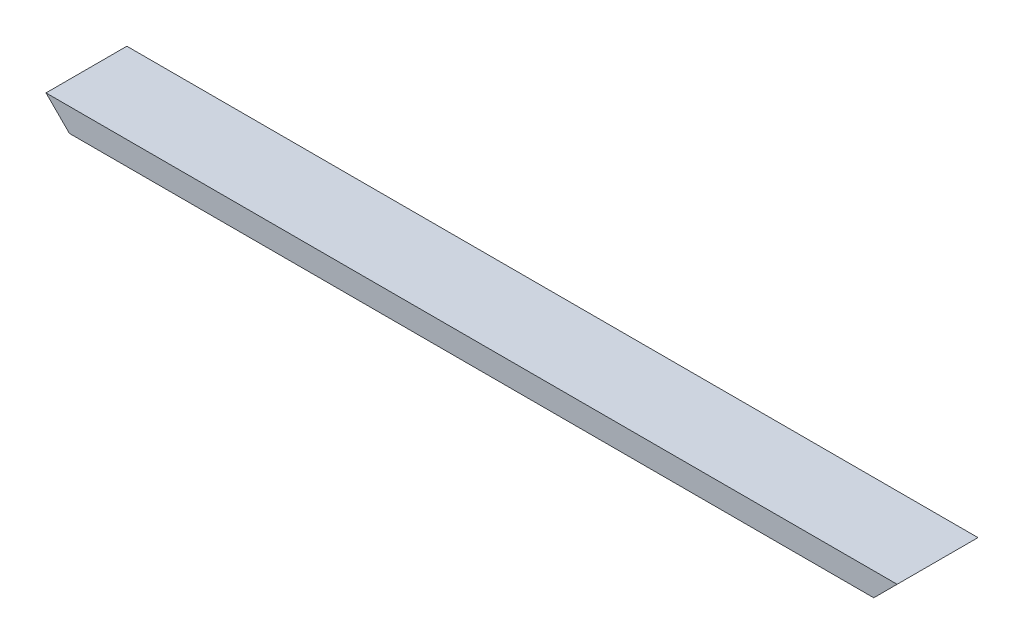
SolidWorks part; units mm, degrees
material "Stainless Steel (ferritic)"
ref_plane "Front Plane" through (0, 0, 0) normal (0, 0, 1) x (1, 0, 0)
ref_plane "Top Plane" through (0, 0, 0) normal (0, 1, 0) x (1, 0, 0)
ref_plane "Right Plane" through (0, 0, 0) normal (1, 0, 0) x (0, 0, -1)
sketch "Sketch1" plane through (0, 0, 0) normal (1, 0, 0) x (0, 0, -1)
  line L0 (-17.5, 4) -> (17.5, 4)
  line L1 (-19, -5.5) -> (19, -5.5)
  line L2 (-19, -5.5) -> (-19, 5.5)
  line L3 (-19, 5.5) -> (19, 5.5)
  line L4 (19, -5.5) -> (19, 5.5)
  line L5 (-19, -5.5) -> (19, 5.5) construction
  line L6 (-19, 5.5) -> (19, -5.5) construction
  line L7 (17.5, -4) -> (17.5, 4)
  line L8 (-17.5, -4) -> (17.5, -4)
  line L9 (-17.5, -4) -> (-17.5, 4)
  point P0 (0, 0)
  dimension "D1" = 38
  dimension "D2" = 11
  dimension "D3" = 1.5
extrude "Boss-Extrude1" add sketch "Sketch1" along normal blind 400
sketch "Sketch2" plane through (0, 0, -19) normal (0, 0, -1) x (-1, 0, 0)
  line L0 (0, 5.5) -> (-11, -5.5)
  line L1 (-400, -5.5) -> (0, -5.5) construction
  line L2 (0, -5.5) -> (0, 5.5) construction
  dimension "D1" = 45
extrude "Cut-Extrude1" cut sketch "Sketch2" against normal through all and the other way through all
sketch "Sketch3" plane through (0, 0, -19) normal (0, 0, -1) x (-1, 0, 0)
  line L0 (-400, 5.5) -> (-389, -5.5)
  line L1 (-400, -5.5) -> (-11, -5.5) construction
  line L2 (-400, -5.5) -> (-400, 5.5) construction
  dimension "D1" = 45
extrude "Cut-Extrude3" cut sketch "Sketch3" against normal through all and the other way through all flip side to cut
sketch "Sketch4" plane through (0, -5.5, 0) normal (0, -1, 0) x (1, 0, 0)
  line L0 (200, 19) -> (200, -19) construction
  line L1 (389, 19) -> (11, 19) construction
  line L2 (389, -19) -> (11, -19) construction
sketch "Sketch5" plane through (0, 5.5, 0) normal (0, 1, 0) x (1, 0, 0)
  line L0 (200, 19) -> (200, -19) construction
